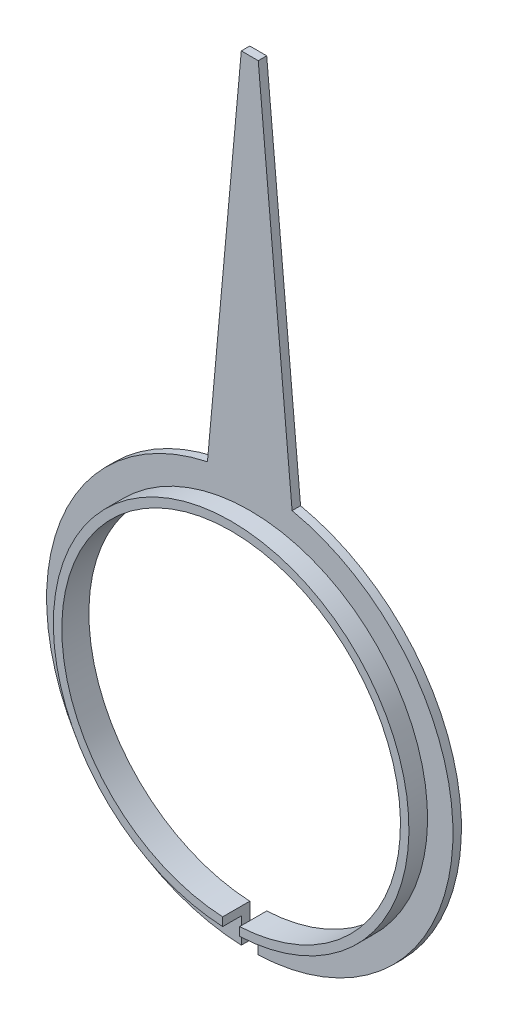
SolidWorks part; units mm, degrees
ref_plane "Alzado" through (0, 0, 0) normal (0, 0, 1) x (1, 0, 0)
ref_plane "Planta" through (0, 0, 0) normal (0, 1, 0) x (1, 0, 0)
ref_plane "Vista lateral" through (0, 0, 0) normal (1, 0, 0) x (0, 0, -1)
sketch "Sketch1" plane through (0, 0, 0) normal (0, 0, 1) x (1, 0, 0)
  line L0 (0, -1000) -> (0, 49000) construction
  line L1 (-1000, 0) -> (49000, 0) construction
  line L2 (-999.9122, 6.75) -> (49000.0878, 6.75) construction
  line L4 (0.1, -996.6733) -> (0.1, 49003.3267) construction
  line L5 (0, 6.75) -> (0.1, 6.75)
  line L6 (0.5, -996.9278) -> (0.5, 49003.0722) construction
  line L7 (0.1, 6.75) -> (0.5, 2.3473)
  line L8 (-0.1, 6.75) -> (-0.5, 2.3473)
  line L9 (0, 6.75) -> (-0.1, 6.75)
  arc A0 (-0.5, 2.3473) -> (0.5, 2.3473) centre (0, 0) ccw
  point P12 (0.1, 6.75)
  point P15 (0.5, 2.3473)
  dimension "D1" = 4.8
  dimension "D2" = 6.75
  dimension "D4" = 0.1
  dimension "D5" = 0.5
extrude "Boss-Extrude1" add sketch "Sketch1" along normal blind 0.1
sketch "Sketch3" plane through (0, 0, 0) normal (0, 0, 1) x (1, 0, 0)
  circle A0 centre (0, 0) radius 2.1
  dimension "D1" = 4.2
extrude "Boss-Extrude2" add sketch "Sketch3" along normal blind 0.32
sketch "Sketch4" plane through (0, 0, 0) normal (0, 0, 1) x (1, 0, 0)
  circle A0 centre (0, 0) radius 2
  dimension "D1" = 4
extrude "Cut-Extrude1" cut sketch "Sketch4" along normal through all
sketch "Sketch5" plane through (0, 0, 0) normal (0, 0, 1) x (1, 0, 0)
  line L0 (0, -1000) -> (0, 49000) construction
  line L1 (0.1, -1000.8892) -> (0.1, 48999.1108) construction
  line L2 (-0.1, -1.811) -> (0.1, -1.811)
  line L3 (0.1, -1.811) -> (0.1, -2.7082)
  line L4 (0.1, -2.7082) -> (-0.1, -2.7082)
  line L5 (-0.1, -1.811) -> (-0.1, -2.7082)
  point P10 (0, -2.7082)
  point P11 (0, -1.811)
  dimension "D1" = 0.1
extrude "Cut-Extrude2" cut sketch "Sketch5" along normal through all
